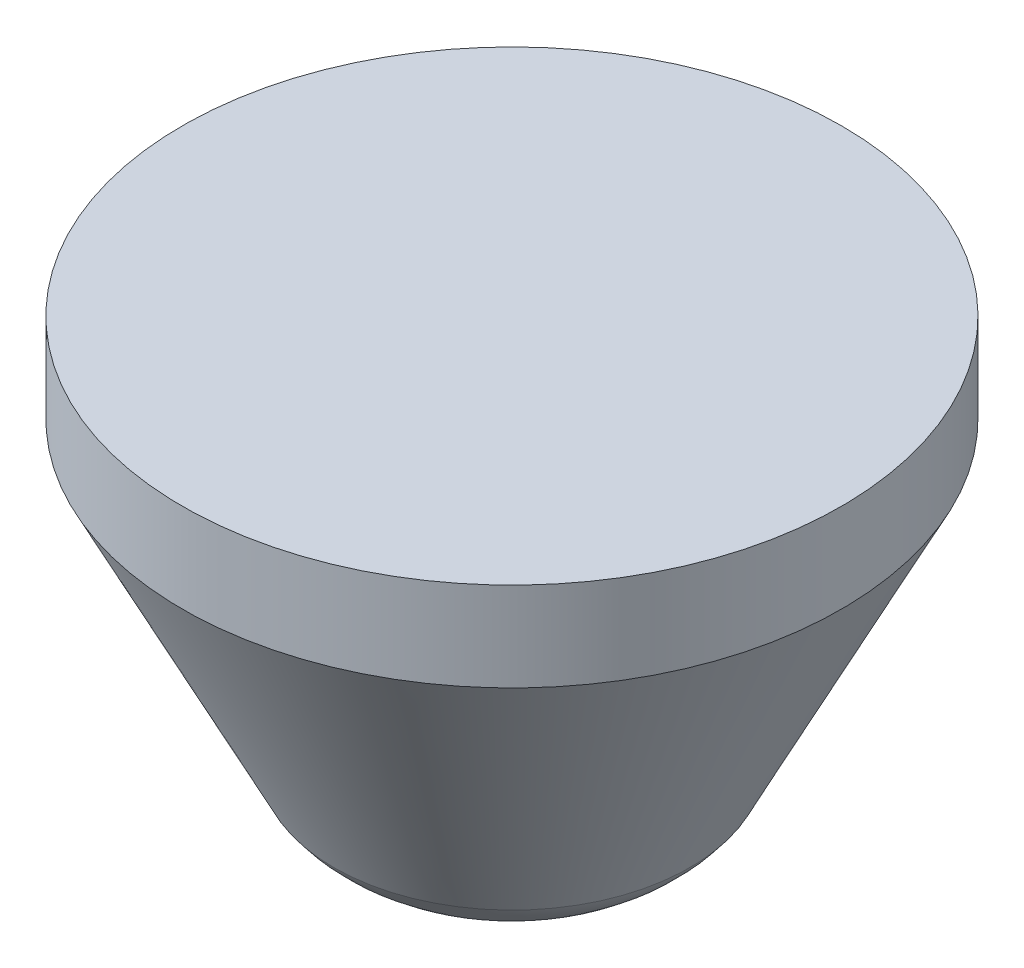
SolidWorks part; units mm, degrees
ref_plane "Alzado" through (0, 0, 0) normal (0, 0, 1) x (1, 0, 0)
ref_plane "Planta" through (0, 0, 0) normal (0, 1, 0) x (1, 0, 0)
ref_plane "Vista lateral" through (0, 0, 0) normal (1, 0, 0) x (0, 0, -1)
sketch "Croquis1" plane through (0, 0, 0) normal (0, 0, 1) x (1, 0, 0)
  line L0 (0, 0) -> (0, 10)
  line L1 (0, 10) -> (7.4, 10)
  line L3 (1.5433, 0) -> (0, 0)
  line L4 (7.4, 10) -> (7.4, 8)
  line L5 (7.4, 8) -> (3.9966, 1.2733)
  arc A0 (3.9966, 1.2733) -> (1.5433, 0) centre (1.5433, 3) cw
  point P7 (3.5, 0)
  dimension "D4" = 3
  dimension "D1" = 7.4
  dimension "D2" = 10
  dimension "D3" = 3.5
  dimension "D5" = 2
  dimension "D6" = 26.837
revolve "Revolución1" add sketch "Croquis1" angle 360 about L0
